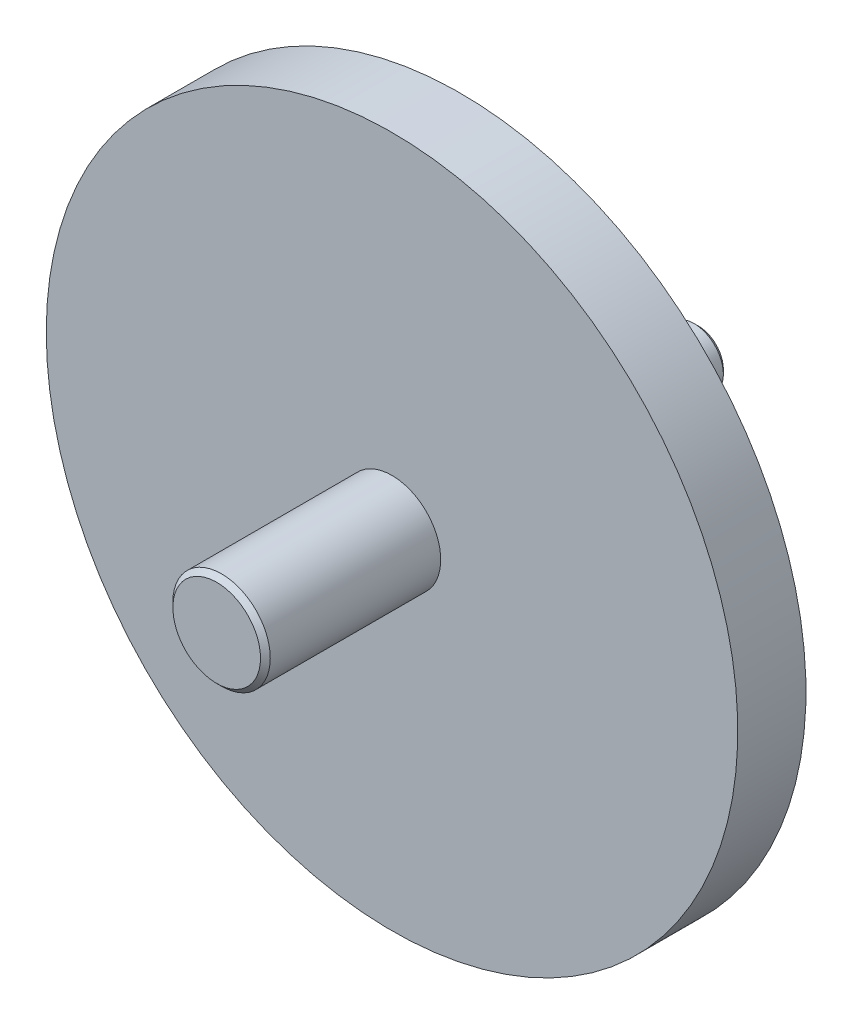
SolidWorks part; units mm, degrees
ref_plane "Alzado" through (0, 0, 0) normal (0, 0, 1) x (1, 0, 0)
ref_plane "Planta" through (0, 0, 0) normal (0, 1, 0) x (1, 0, 0)
ref_plane "Vista lateral" through (0, 0, 0) normal (1, 0, 0) x (0, 0, -1)
sketch "Croquis1" plane through (0, 0, 0) normal (1, 0, 0) x (0, 0, -1)
  line L0 (0, 0) -> (0, 5)
  line L1 (0, 5) -> (18, 5)
  line L2 (18, 5) -> (18, 35.5)
  line L3 (18, 35.5) -> (25, 35.5)
  line L4 (25, 35.5) -> (25, 5)
  line L7 (33, 5) -> (40.4641, 3)
  line L9 (49.4641, 3) -> (49.4641, 0)
  line L10 (49.4641, 0) -> (0, 0)
  line L11 (26.6, 5) -> (33, 5)
  line L12 (49.4641, 3) -> (40.4641, 3)
  arc A0 (25, 5) -> (26.6, 5) centre (25.8, 5) ccw
  dimension "D1" = 0.8
  dimension "D2" = 5
  dimension "D3" = 75
  dimension "D4" = 3
  dimension "D5" = 8
  dimension "D6" = 9
  dimension "D7" = 7
  dimension "D8" = 35.5
  dimension "D9" = 18
  dimension "D10" = 5
revolve "Revolución1" add sketch "Croquis1" angle 360 about L10
cosmetic thread "Rosca cosmética1" parameters "D1"=15, "D2"=8.891
chamfer "Chaflán1" distance 0.45 angle 45 1 edges at (-3, 0, -49.4641)
chamfer "Chaflán2" distance 0.5 angle 45 1 edges at (-5, 0, 0)
